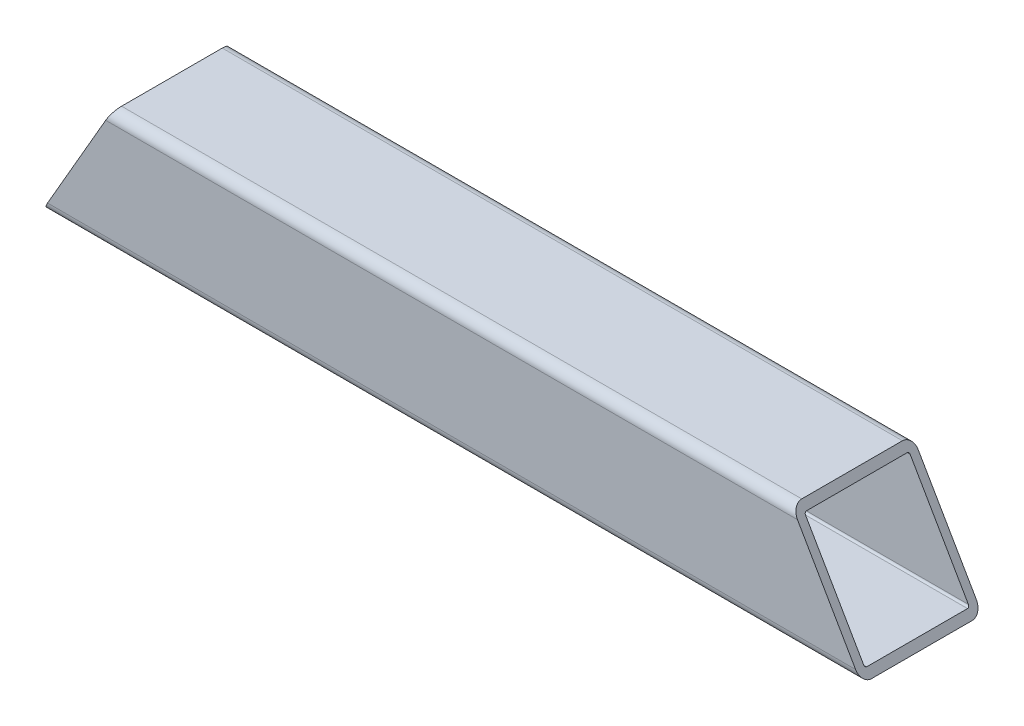
SolidWorks part; units mm, degrees
ref_plane "Front Plane" through (0, 0, 0) normal (0, 0, 1) x (1, 0, 0)
ref_plane "Top Plane" through (0, 0, 0) normal (0, 1, 0) x (1, 0, 0)
ref_plane "Right Plane" through (0, 0, 0) normal (1, 0, 0) x (0, 0, -1)
sketch "Sketch1" plane through (0, 0, 0) normal (1, 0, 0) x (0, 0, -1)
  line L1 (-15.875, 19.05) -> (15.875, 19.05)
  line L2 (-19.05, 15.875) -> (-19.05, -15.875)
  line L3 (-15.875, -19.05) -> (15.875, -19.05)
  line L4 (19.05, 15.875) -> (19.05, -15.875)
  line L5 (-19.05, 19.05) -> (19.05, -19.05) construction
  line L6 (-19.05, -19.05) -> (19.05, 19.05) construction
  arc A0 (-19.05, -15.875) -> (-15.875, -19.05) centre (-15.875, -15.875) ccw
  arc A1 (15.875, -19.05) -> (19.05, -15.875) centre (15.875, -15.875) ccw
  arc A2 (19.05, 15.875) -> (15.875, 19.05) centre (15.875, 15.875) ccw
  arc A3 (-15.875, 19.05) -> (-19.05, 15.875) centre (-15.875, 15.875) ccw
  point P0 (0, 0)
  dimension "D3" = 3.175
  dimension "D1" = 38.1
  dimension "D2" = 38.1
extrude "Extrude-Thin1" add sketch "Sketch1" along normal mid plane 258.445 thin
sketch "Sketch2" plane through (0, 0, 19.05) normal (0, 0, 1) x (1, 0, 0)
  line L0 (-129.2225, -19.05) -> (-107.2255, 19.05)
  line L1 (129.2225, 19.05) -> (-129.2225, 19.05) construction
  line L2 (-129.2225, 15.875) -> (-129.2225, -15.875) construction
  dimension "D1" = 30
extrude "Cut-Extrude1" cut sketch "Sketch2" against normal through all and the other way through all
sketch "Sketch3" plane through (0, 0, 19.05) normal (0, 0, 1) x (1, 0, 0)
  line L0 (129.2225, -19.05) -> (107.2255, 19.05)
  line L1 (129.2225, 19.05) -> (-107.2255, 19.05) construction
  line L2 (129.2225, 15.875) -> (129.2225, -15.875) construction
  dimension "D1" = 30
extrude "Cut-Extrude2" cut sketch "Sketch3" against normal through all and the other way through all flip side to cut
